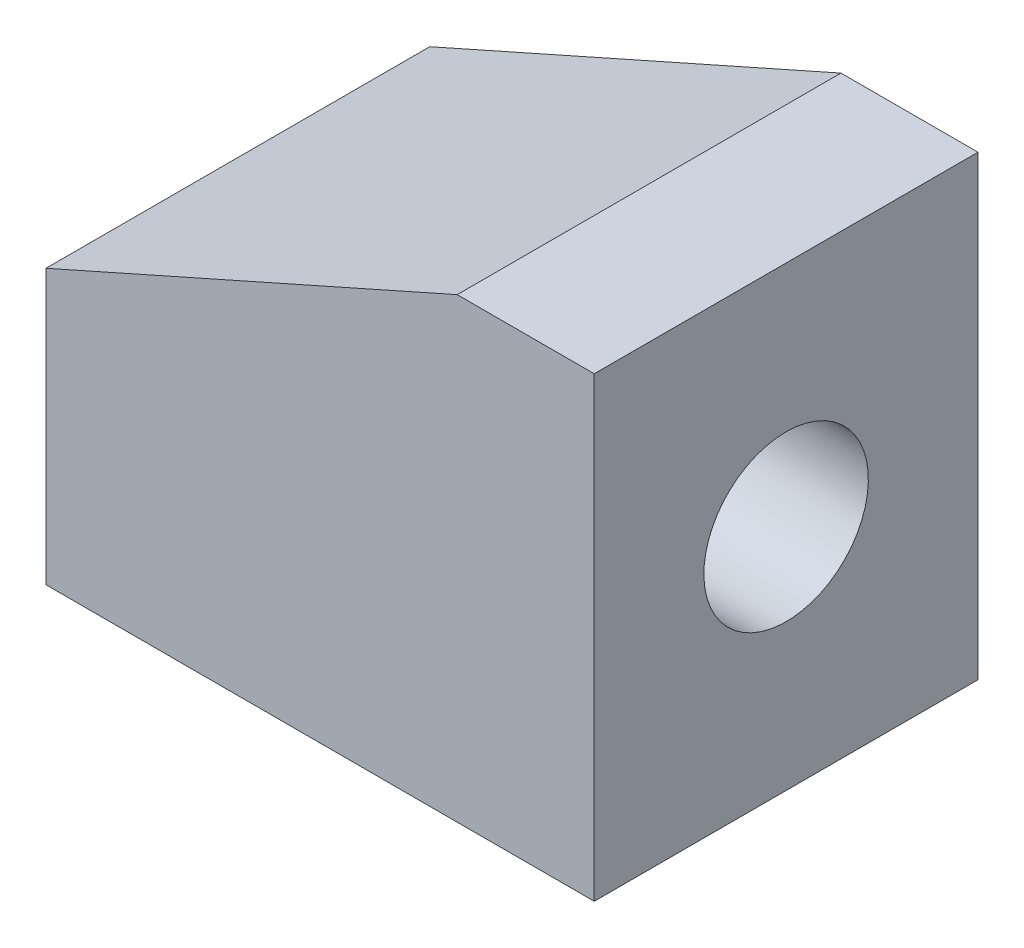
SolidWorks part; units mm, degrees
ref_plane "Front Plane" through (0, 0, 0) normal (0, 0, 1) x (1, 0, 0)
ref_plane "Top Plane" through (0, 0, 0) normal (0, 1, 0) x (1, 0, 0)
ref_plane "Right Plane" through (0, 0, 0) normal (1, 0, 0) x (0, 0, -1)
sketch "Sketch1" plane through (0, 0, 0) normal (0, 0, 1) x (1, 0, 0)
  line L0 (0, 0) -> (-60, 0)
  line L1 (-60, 0) -> (-60, 30)
  line L2 (-60, 30) -> (-15, 50)
  line L3 (-15, 50) -> (0, 50)
  line L4 (0, 50) -> (0, 0)
  dimension "D1" = 60
  dimension "D2" = 50
  dimension "D3" = 15
  dimension "D4" = 30
extrude "Boss-Extrude1" add sketch "Sketch1" along normal mid plane 42
sketch "Sketch2" plane through (0, 0, 0) normal (1, 0, 0) x (0, 0, -1)
  line L0 (-21, 0) -> (21, 0) construction
  circle A0 centre (0, 25) radius 9
  dimension "D1" = 18
  dimension "D2" = 25
extrude "Cut-Extrude1" cut sketch "Sketch2" against normal blind 40
